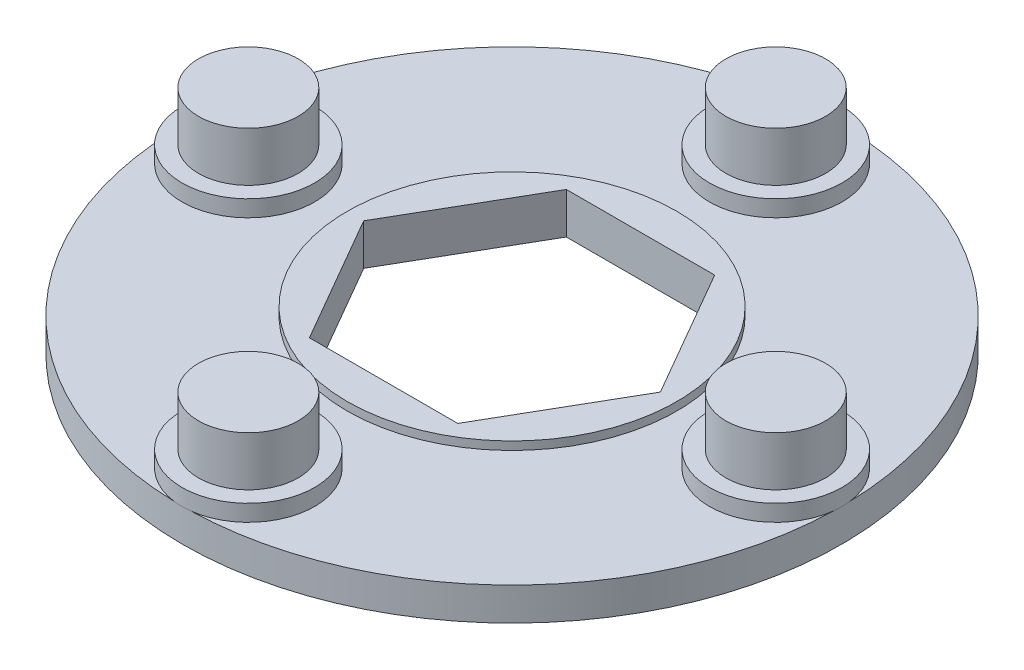
SolidWorks part; units mm, degrees
material "ABS"
ref_plane "Plan de face" through (0, 0, 0) normal (0, 0, 1) x (1, 0, 0)
ref_plane "Plan de dessus" through (0, 0, 0) normal (0, 1, 0) x (1, 0, 0)
ref_plane "Plan de droite" through (0, 0, 0) normal (1, 0, 0) x (0, 0, -1)
sketch "Esquisse1" plane through (0, 0, 0) normal (0, 1, 0) x (1, 0, 0)
  circle A0 centre (0, 0) radius 16 construction
  circle A1 centre (0, 0) radius 20
  circle A2 centre (0, 16) radius 4 construction
  dimension "D1" = 32
  dimension "D2" = 8
  dimension "D3" = 40
extrude "Boss.-Extru.1" add sketch "Esquisse1" along normal blind 2
sketch "Esquisse2" plane through (0, 2, 0) normal (0, 1, 0) x (1, 0, 0)
  circle A0 centre (0, 0) radius 16 construction
  circle A1 centre (0, 16) radius 3.025
  circle A2 centre (16, 0) radius 3.025
  circle A3 centre (0, -16) radius 3.025
  circle A4 centre (-16, 0) radius 3.025
  point P15 (0, 0)
  dimension "D1" = 6.05
  dimension "D2" = 32
  dimension "D3" = 4
extrude "Boss.-Extru.2" add sketch "Esquisse2" along normal blind 4
sketch "Esquisse4" plane through (0, 2, 0) normal (0, 1, 0) x (1, 0, 0)
  circle A0 centre (0, 0) radius 10
  dimension "D1" = 20
extrude "Boss.-Extru.3" add sketch "Esquisse4" along normal blind 0.5
sketch "Esquisse3" plane through (0, 2.5, 0) normal (0, 1, 0) x (1, 0, 0)
  line L0 (0, 16) -> (0, 0) construction
  line L1 (4.5, -7.7942) -> (9, 0)
  line L2 (9, 0) -> (4.5, 7.7942)
  line L3 (4.5, 7.7942) -> (-4.5, 7.7942)
  line L4 (-4.5, 7.7942) -> (-9, 0)
  line L5 (-9, 0) -> (-4.5, -7.7942)
  line L6 (-4.5, -7.7942) -> (4.5, -7.7942)
  circle A0 centre (0, 0) radius 7.7942 construction
  circle A1 centre (0, 0) radius 9 construction
  dimension "D1" = 18
extrude "Enlèv. mat.-Extru.1" cut sketch "Esquisse3" against normal blind 6
sketch "Esquisse5" plane through (0, 2, 0) normal (0, 1, 0) x (1, 0, 0)
  circle A1 centre (16, 0) radius 4.025
  circle A2 centre (0, 16) radius 4.025
  circle A3 centre (0, 16) radius 4.025
  circle A4 centre (0, -16) radius 4.025
  circle A5 centre (-16, 0) radius 4.025
  point P12 (0, 0)
  point P13 (0, 0)
  point P14 (0, 0)
  point P15 (0, 0)
  dimension "D1" = 1
  dimension "D2" = 4
extrude "Boss.-Extru.4" add sketch "Esquisse5" along normal blind 1
